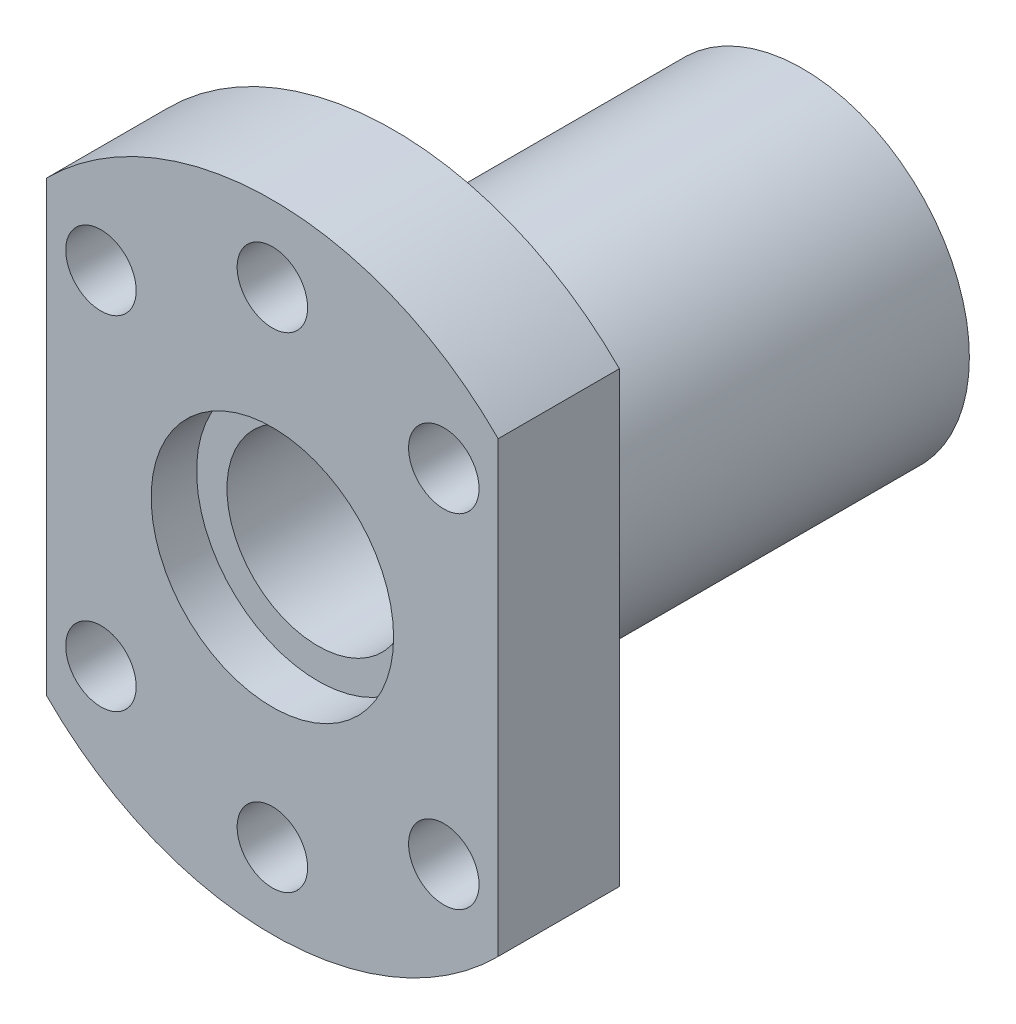
SolidWorks part; units mm, degrees
material "Plain Carbon Steel"
ref_plane "Front Plane" through (0, 0, 0) normal (0, 0, 1) x (1, 0, 0)
ref_plane "Top Plane" through (0, 0, 0) normal (0, 1, 0) x (1, 0, 0)
ref_plane "Right Plane" through (0, 0, 0) normal (1, 0, 0) x (0, 0, -1)
sketch "Sketch1" plane through (0, 0, 0) normal (1, 0, 0) x (0, 0, -1)
  line L0 (-27, 0) -> (-1.1455, 0) construction
  line L1 (14.5, 6) -> (-14.5, 6)
  line L2 (-17.5, 8) -> (-17.5, 21)
  line L3 (-17.5, 21) -> (-9.5, 21)
  line L4 (-9.5, 21) -> (-9.5, 11)
  line L5 (-9.5, 11) -> (17.5, 11)
  line L6 (17.5, 11) -> (17.5, 8)
  line L7 (0, 6) -> (0, 0) construction
  line L8 (14.5, 6) -> (14.5, 8)
  line L11 (-17.5, 8) -> (-14.5, 8)
  line L12 (-14.5, 6) -> (-14.5, 8)
  line L13 (17.5, 8) -> (14.5, 8)
  dimension "D1" = 27
  dimension "D2" = 8
  dimension "D3" = 21
  dimension "D4" = 12
  dimension "D5" = 22
  dimension "D6" = 8
  dimension "D7" = 3
revolve "Revolve1" add sketch "Sketch1" angle 360 about L0
sketch "Sketch2" plane through (0, 0, 0) normal (0, 1, 0) x (1, 0, 0)
  line L0 (-21, -17.5) -> (21, -17.5) construction
  line L1 (-21, -9.5) -> (-14.9, -9.5)
  line L2 (-21, -9.5) -> (-21, -17.5)
  line L3 (-21, -17.5) -> (-14.9, -17.5)
  line L4 (-14.9, -9.5) -> (-14.9, -17.5)
  line L6 (21, -9.5) -> (14.9, -9.5)
  line L7 (21, -9.5) -> (21, -17.5)
  line L8 (21, -17.5) -> (14.9, -17.5)
  line L9 (14.9, -9.5) -> (14.9, -17.5)
  dimension "D1" = 29.8
extrude "Cut-Extrude1" cut sketch "Sketch2" against normal through all both and the other way through all
sketch "Sketch3" plane through (0, 0, 17.5) normal (0, 0, 1) x (1, 0, 0)
  line L0 (0, 16) -> (0, 0) construction
  circle A0 centre (0, 16) radius 2.325
  circle A1 centre (11.3137, 11.3137) radius 2.325
  circle A2 centre (16, 0) radius 2.325 construction
  circle A3 centre (11.3137, -11.3137) radius 2.325
  circle A4 centre (0, -16) radius 2.325
  circle A5 centre (-11.3137, -11.3137) radius 2.325
  circle A6 centre (-16, 0) radius 2.325 construction
  circle A7 centre (-11.3137, 11.3137) radius 2.325
  point P19 (0, 0)
  dimension "D2" = 4.65
  dimension "D1" = 16
  dimension "D3" = 8
extrude "Cut-Extrude2" cut sketch "Sketch3" against normal blind 10
